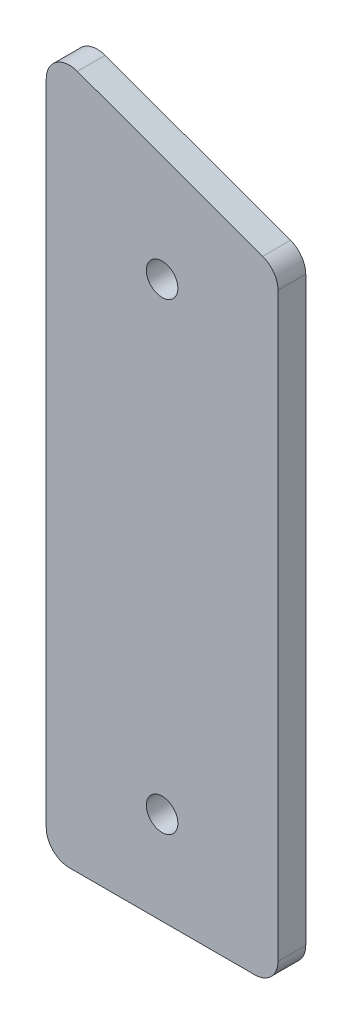
SolidWorks part; units mm, degrees
ref_plane "Plane1" through (0, 0, 0) normal (0, 0, 1) x (1, 0, 0)
ref_plane "Plane2" through (0, 0, 0) normal (0, 1, 0) x (1, 0, 0)
ref_plane "Plane3" through (0, 0, 0) normal (1, 0, 0) x (0, 0, -1)
sketch "Sketch1" plane through (0, 0, 0) normal (0, 0, 1) x (1, 0, 0)
  line L0 (0, 0) -> (0, 40) construction
  line L1 (-20, 0) -> (20, 0)
  line L2 (-25, 5) -> (-25, 145)
  line L3 (-18.2899, 149.6985) -> (21.7101, 135.1397)
  line L4 (25, 5) -> (25, 130.4412)
  circle A1 centre (0, 120) radius 3.4
  arc A2 (25, 5) -> (20, 0) centre (20, 5) cw
  arc A3 (-25, 5) -> (-20, 0) centre (-20, 5) ccw
  arc A4 (-18.2899, 149.6985) -> (-25, 145) centre (-20, 145) ccw
  arc A5 (25, 130.4412) -> (21.7101, 135.1397) centre (20, 130.4412) ccw
  circle A6 centre (0, 20) radius 3.4
  dimension "D3" = 6.8
  dimension "D6" = 5
  dimension "D2" = 150
  dimension "D5" = 25
  dimension "D1" = 50
  dimension "D4" = 20
  dimension "D7" = 70
  dimension "D8" = 100
extrude "Base-Extrude" add sketch "Sketch1" along normal blind 6
cosmetic thread "Cosmetic Thread1" parameters "D2"=8
cosmetic thread "Cosmetic Thread2" parameters "D2"=8
